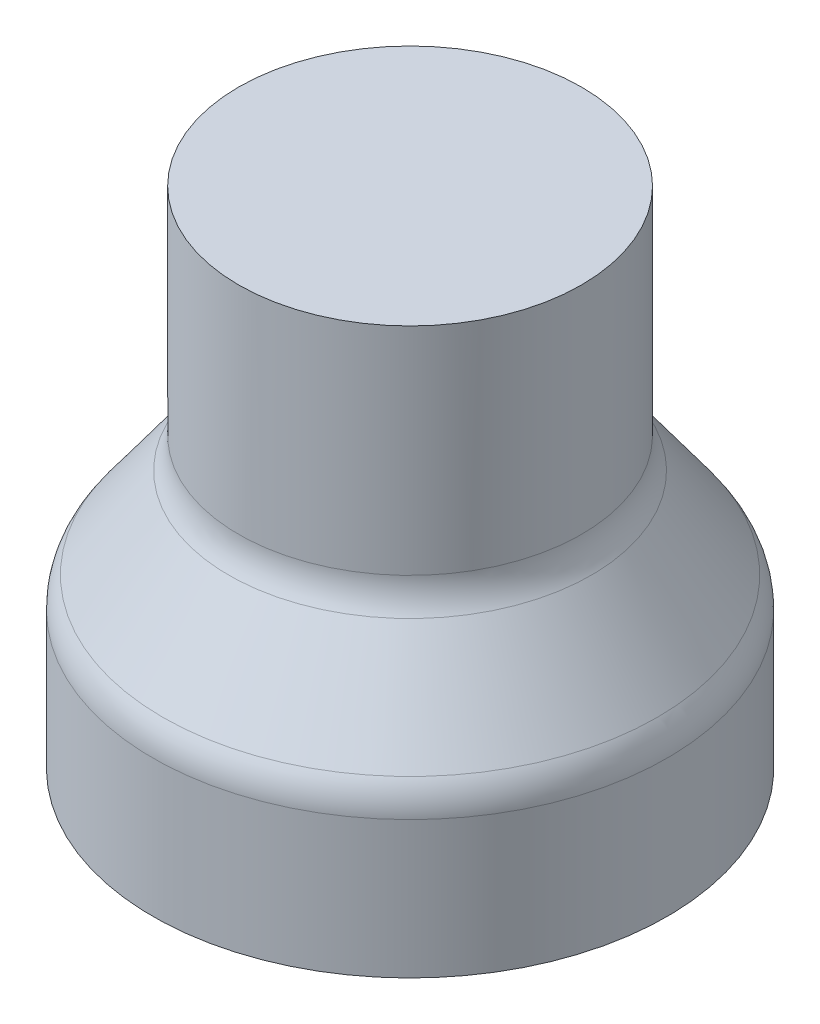
SolidWorks part; units mm, degrees
ref_plane "Front Plane" through (0, 0, 0) normal (0, 0, 1) x (1, 0, 0)
ref_plane "Top Plane" through (0, 0, 0) normal (0, 1, 0) x (1, 0, 0)
ref_plane "Right Plane" through (0, 0, 0) normal (1, 0, 0) x (0, 0, -1)
sketch "Sketch1" plane through (0, 0, 0) normal (0, 1, 0) x (1, 0, 0)
  circle A0 centre (0, 0) radius 3.75
  dimension "D1" = 7.5
ref_plane "Plane1" through (0, 6.2, 0) normal (0, 1, 0) x (1, 0, 0)
sketch "Sketch2" plane through (0, 6.2, 0) normal (0, 1, 0) x (1, 0, 0)
  circle A0 centre (0, 0) radius 2.5
  dimension "D1" = 5
sketch "Sketch6" plane through (0, 0, 0) normal (1, 0, 0) x (0, 0, -1)
  line L0 (-3.75, 0) -> (-3.75, 2)
  line L1 (-3.6055, 2.4426) -> (-2.6445, 3.7574)
  line L2 (-2.5, 4.2) -> (-2.5, 6.2)
  arc A0 (-2.5, 4.2) -> (-2.6445, 3.7574) centre (-3.25, 4.2) cw
  arc A1 (-3.75, 2) -> (-3.6055, 2.4426) centre (-3, 2) cw
  dimension "D2" = 2
  dimension "D3" = 2
sketch "Sketch7" plane through (0, 0, 0) normal (1, 0, 0) x (0, 0, -1)
  line L0 (0, -0.2276) -> (0, 2.526)
revolve "Revolve-Thin2" add sketch "Sketch6" angle 360 about L0
sketch "Sketch8" plane through (0, 6.2, 0) normal (0, 1, 0) x (1, 0, 0)
  circle A0 centre (0, 0) radius 2.5
  circle A2 centre (0, 0) radius 2.5 construction
extrude "Boss-Extrude1" add sketch "Sketch8" along normal blind 1.15
